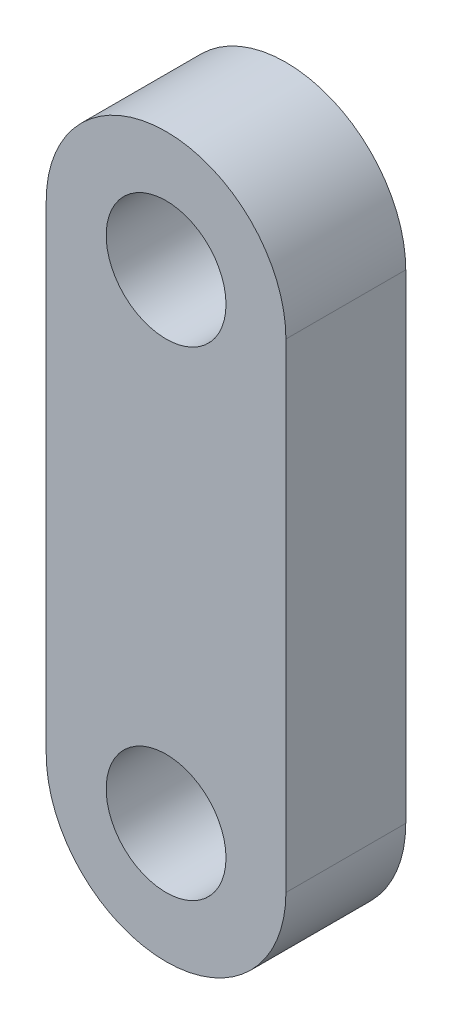
SolidWorks part; units mm, degrees
ref_plane "Front Plane" through (0, 0, 0) normal (0, 0, 1) x (1, 0, 0)
ref_plane "Top Plane" through (0, 0, 0) normal (0, 1, 0) x (1, 0, 0)
ref_plane "Right Plane" through (0, 0, 0) normal (1, 0, 0) x (0, 0, -1)
sketch "Sketch1" plane through (0, 0, 0) normal (0, 0, 1) x (1, 0, 0)
  line L0 (0, 0) -> (0, 25.4) construction
  line L1 (-6.35, 25.4) -> (-6.35, 0)
  line L2 (6.35, 25.4) -> (6.35, 0)
  circle A0 centre (0, 0) radius 3.175
  circle A1 centre (0, 25.4) radius 3.175
  arc A2 (6.35, 25.4) -> (-6.35, 25.4) centre (0, 25.4) ccw
  arc A3 (-6.35, 0) -> (6.35, 0) centre (0, 0) ccw
  dimension "D2" = 6.35
  dimension "D3" = 6.35
  dimension "D4" = 12.7
  dimension "D5" = 12.7
  dimension "D1" = 25.4
extrude "Boss-Extrude1" add sketch "Sketch1" along normal blind 6.35
